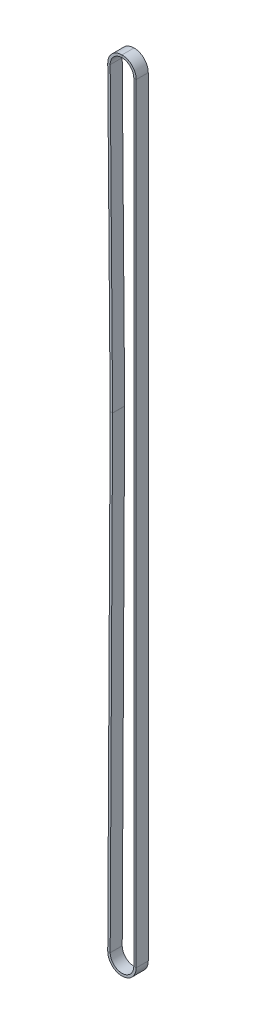
SolidWorks part; units mm, degrees
ref_plane "Front Plane" through (0, 0, 0) normal (0, 0, 1) x (1, 0, 0)
ref_plane "Top Plane" through (0, 0, 0) normal (0, 1, 0) x (1, 0, 0)
ref_plane "Right Plane" through (0, 0, 0) normal (1, 0, 0) x (0, 0, -1)
sketch "Sketch2" plane through (0, 0, 0) normal (0, 0, 1) x (1, 0, 0)
  line L0 (0, 0) -> (1, 0) construction
  line L1 (0, 0) -> (0, 1) construction
  line L2 (-7.218, 0.0375) -> (-5.727, 286.7538)
  line L3 (-5.7271, 286.7892) -> (-7.2178, 470.6035)
  line L4 (7.2181, 470.662) -> (7.2181, 0)
  arc A0 (7.2181, 0) -> (-7.218, 0.0375) centre (0, 0) cw
  arc A1 (-5.727, 286.7538) -> (-5.7271, 286.7892) centre (-8.382, 286.7676) ccw
  arc A2 (-7.2178, 470.6035) -> (7.2181, 470.662) centre (0, 470.662) cw
sketch "Sketch3" plane through (0, 0, 0) normal (1, 0, 0) x (0, 0, -1)
  line L0 (0, 477.8801) -> (0, 470.6035) construction
  line L1 (0, 479.3801) -> (7.366, 479.3801)
  line L2 (0, 479.3801) -> (0, 477.8801)
  line L3 (0, 477.8801) -> (7.366, 477.8801)
  line L4 (7.366, 479.3801) -> (7.366, 477.8801)
  dimension "D1" = 7.366
  dimension "D2" = 1.5
sweep "Sweep1" add profiles "Sketch3" path "Sketch2"
